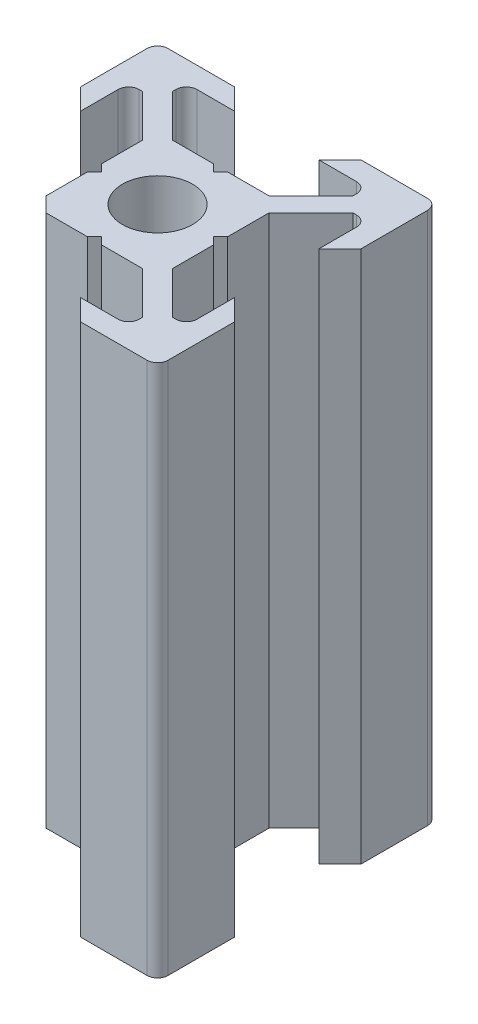
SolidWorks part; units mm, degrees
ref_plane "Face" through (0, 0, 0) normal (0, 0, 1) x (1, 0, 0)
ref_plane "Dessus" through (0, 0, 0) normal (0, 1, 0) x (1, 0, 0)
ref_plane "Droite" through (0, 0, 0) normal (1, 0, 0) x (0, 0, -1)
sketch "Esquisse1" plane through (0, 0, 0) normal (0, 1, 0) x (1, 0, 0)
  line L0 (0, 0) -> (0, 10) construction
  line L1 (0, 0) -> (-10, 0) construction
  line L2 (-10, 0) -> (-10, 10) construction
  line L3 (-10, 10) -> (0, 10) construction
  line L4 (0, 4) -> (-0.5, 4.5)
  line L5 (-0.5, 4.5) -> (-3.4393, 4.5)
  line L6 (-3.4393, 4.5) -> (-6.4393, 7.5)
  line L7 (-6.4393, 7.5) -> (-6.4393, 8.5)
  line L8 (-6.4393, 8.5) -> (-3, 8.5)
  line L9 (-3, 8.5) -> (-4.5, 10)
  line L10 (-4.5, 10) -> (-10, 10)
  line L11 (0, 0) -> (-10, 10) construction
  line L12 (-10, 4.5) -> (-10, 10)
  line L13 (-8.5, 3) -> (-10, 4.5)
  line L14 (-8.5, 6.4393) -> (-8.5, 3)
  line L15 (-7.5, 6.4393) -> (-8.5, 6.4393)
  line L16 (-4.5, 3.4393) -> (-7.5, 6.4393)
  line L17 (-4.5, 0.5) -> (-4.5, 3.4393)
  line L18 (-4, 0) -> (-4.5, 0.5)
  line L19 (0, -4) -> (-0.5, -4.5)
  line L20 (-0.5, -4.5) -> (-3.4393, -4.5)
  line L21 (-4, 0) -> (-4.5, -0.5)
  line L22 (-4.5, -0.5) -> (-4.5, -3.4393)
  line L23 (-4.5, -3.4393) -> (-7.5, -6.4393)
  line L24 (-3.4393, -4.5) -> (-6.4393, -7.5)
  line L25 (-3, -8.5) -> (-4.5, -10)
  line L26 (-6.4393, -8.5) -> (-3, -8.5)
  line L27 (-6.4393, -7.5) -> (-6.4393, -8.5)
  line L28 (-7.5, -6.4393) -> (-8.5, -6.4393)
  line L29 (-4.5, -10) -> (-10, -10)
  line L30 (-10, -4.5) -> (-10, -10)
  line L31 (-8.5, -3) -> (-10, -4.5)
  line L32 (-8.5, -6.4393) -> (-8.5, -3)
  line L33 (8.5, -6.4393) -> (8.5, -3)
  line L34 (8.5, -3) -> (10, -4.5)
  line L35 (10, -4.5) -> (10, -10)
  line L36 (4.5, -10) -> (10, -10)
  line L37 (7.5, -6.4393) -> (8.5, -6.4393)
  line L38 (6.4393, -7.5) -> (6.4393, -8.5)
  line L39 (6.4393, -8.5) -> (3, -8.5)
  line L40 (3, -8.5) -> (4.5, -10)
  line L41 (3.4393, -4.5) -> (6.4393, -7.5)
  line L42 (4.5, -3.4393) -> (7.5, -6.4393)
  line L43 (4.5, -0.5) -> (4.5, -3.4393)
  line L44 (4, 0) -> (4.5, -0.5)
  line L45 (0.5, -4.5) -> (3.4393, -4.5)
  line L46 (0, -4) -> (0.5, -4.5)
  line L47 (4, 0) -> (4.5, 0.5)
  line L48 (4.5, 0.5) -> (4.5, 3.4393)
  line L49 (4.5, 3.4393) -> (7.5, 6.4393)
  line L50 (7.5, 6.4393) -> (8.5, 6.4393)
  line L51 (8.5, 6.4393) -> (8.5, 3)
  line L52 (8.5, 3) -> (10, 4.5)
  line L53 (10, 4.5) -> (10, 10)
  line L54 (4.5, 10) -> (10, 10)
  line L55 (3, 8.5) -> (4.5, 10)
  line L56 (6.4393, 8.5) -> (3, 8.5)
  line L57 (6.4393, 7.5) -> (6.4393, 8.5)
  line L58 (3.4393, 4.5) -> (6.4393, 7.5)
  line L59 (0.5, 4.5) -> (3.4393, 4.5)
  line L60 (0, 4) -> (0.5, 4.5)
  circle A0 centre (0, 0) radius 2.5
  dimension "D10" = 5
  dimension "D1" = 10
  dimension "D2" = 45
  dimension "D3" = 45
  dimension "D4" = 1.5
  dimension "D5" = 7
  dimension "D6" = 1
  dimension "D7" = 4.5
  dimension "D8" = 0.5
  dimension "D9" = 0.75
extrude "Extrusion1" add sketch "Esquisse1" along normal blind 38
fillet "Congé1" radius 0.75 12 edges at (-8.5, 19, -6.4393) (-6.4393, 19, -8.5) (8.5, 19, -6.4393) (6.4393, 19, -8.5) (-8.5, 19, 6.4393) (-6.4393, 19, 8.5) (8.5, 19, 6.4393) (6.4393, 19, 8.5) (10, 19, -10) (-10, 19, -10) (-10, 19, 10) (10, 19, 10)
sketch "Esquisse2" plane through (0, 38, 0) normal (0, 1, 0) x (1, 0, 0)
  line L0 (-3.4393, -4.5) -> (-4.5, -3.4393)
  line L1 (-4.5, -3.4393) -> (-8.5, -3)
  line L2 (-8.5, -3) -> (-10, -4.5)
  line L3 (-10, -4.5) -> (-10, -10)
  line L4 (-10, -10) -> (-4.5, -10)
  line L5 (-4.5, -10) -> (-3, -8.5)
  line L6 (-3, -8.5) -> (-3.4393, -4.5)
extrude "Extrusion2" cut sketch "Esquisse2" against normal up to next
